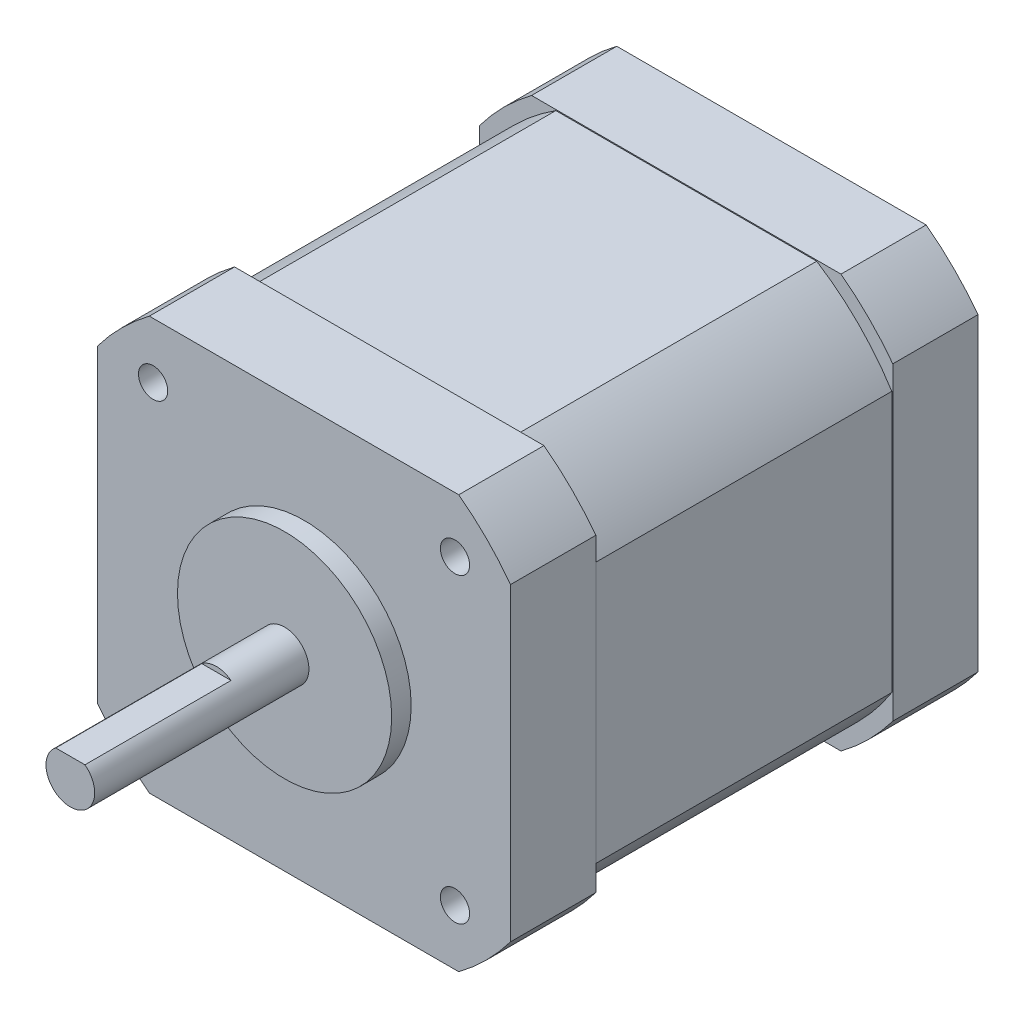
SolidWorks part; units mm, degrees
material "Plain Carbon Steel"
ref_plane "Front" through (0, 0, 0) normal (0, 0, 1) x (1, 0, 0)
ref_plane "Top" through (0, 0, 0) normal (0, 1, 0) x (1, 0, 0)
ref_plane "Right" through (0, 0, 0) normal (1, 0, 0) x (0, 0, -1)
sketch "Sketch1" plane through (0, 0, 0) normal (0, 0, 1) x (1, 0, 0)
  circle A0 centre (0, 0) radius 2.5
  dimension "D1" = 5
extrude "Boss-Extrude1" add sketch "Sketch1" along normal blind 24
sketch "Sketch2" plane through (0, 0, 0) normal (0, 0, -1) x (-1, 0, 0)
  circle A0 centre (0, 0) radius 11
  dimension "D1" = 22
extrude "Boss-Extrude2" add sketch "Sketch2" against normal blind 2
sketch "Sketch3" plane through (0, 0, 0) normal (0, 0, -1) x (-1, 0, 0)
  line L1 (21.209, -21.209) -> (-21.209, -21.209)
  line L2 (21.209, -21.209) -> (21.209, 21.209)
  line L3 (21.209, 21.209) -> (-21.209, 21.209)
  line L4 (-21.209, -21.209) -> (-21.209, 21.209)
  line L5 (21.209, -21.209) -> (-21.209, 21.209) construction
  line L6 (21.209, 21.209) -> (-21.209, -21.209) construction
  point P0 (0, 0)
  dimension "D1" = 42.418
extrude "Boss-Extrude3" add sketch "Sketch3" along normal blind 48
sketch "Sketch4" plane through (0, 0, -48) normal (0, 0, -1) x (-1, 0, 0)
  line L0 (-21.209, -15.888) -> (-21.209, -21.209)
  line L1 (15.888, -21.209) -> (21.209, -21.209)
  line L2 (21.209, 15.888) -> (21.209, 21.209)
  line L3 (-15.888, 21.209) -> (-21.209, 21.209)
  line L4 (-21.209, 21.209) -> (-21.209, -21.209)
  line L5 (-21.209, -21.209) -> (21.209, -21.209)
  line L6 (21.209, -21.209) -> (21.209, 21.209)
  line L7 (21.209, 21.209) -> (-21.209, 21.209)
  line L8 (-21.209, 21.209) -> (-21.209, 15.888)
  line L9 (-21.209, -21.209) -> (-15.888, -21.209)
  line L10 (21.209, -21.209) -> (21.209, -15.888)
  line L11 (21.209, 21.209) -> (15.888, 21.209)
  arc A0 (-21.209, -15.888) -> (-15.888, -21.209) centre (0, 0) ccw
  arc A1 (15.888, -21.209) -> (21.209, -15.888) centre (0, 0) ccw
  arc A2 (21.209, 15.888) -> (15.888, 21.209) centre (0, 0) ccw
  arc A3 (-15.888, 21.209) -> (-21.209, 15.888) centre (0, 0) ccw
  dimension "D2" = 26.5
  dimension "D1" = 0
extrude "Cut-Extrude1" cut sketch "Sketch4" against normal through all
hole_wizard "M3x0.5 Tapped Hole1" positions "Sketch6" profile "Sketch5" tap size "M3x0.5" standard "ANSI Metric"
sketch "Sketch6" plane through (0, 0, 0) normal (0, 0, 1) x (1, 0, 0)
  line L0 (-16.1632, 0) -> (0, 0) construction
  line L1 (0, 0) -> (0, 15.0764) construction
  point P0 (-15.5, 15.5)
  point P11 (-15.5, -15.5)
  point P12 (15.5, -15.5)
  point P13 (15.5, 15.5)
  dimension "D1" = 31
  dimension "D2" = 31
sketch "Sketch5" plane through (-15.5, 15.5, 0) normal (1, 0, 0) x (0, -1, 0)
  line L0 (0, 0) -> (0, 8.2511)
  line L1 (0, 8.2511) -> (1.25, 7.5)
  line L2 (1.25, 7.5) -> (1.25, 6)
  line L3 (1.25, 6) -> (1.5, 6)
  line L4 (1.5, 6) -> (1.5, 0)
  line L5 (1.5, 0) -> (0, 0)
  line L10 (0, 8.2511) -> (-1.25, 7.5) construction
  line L11 (0, -6.35) -> (0, 107.95) construction
  dimension "Tap Drill Dia." = 2.5
  dimension "Tap Drill Depth" = 7.5
  dimension "Thread Major Dia." = 3
  dimension "Thread Depth" = 6
  dimension "Drill Angle" = 118
sketch "Sketch7" plane through (0, 0, 24) normal (0, 0, 1) x (1, 0, 0)
  line L0 (-1.5, 2) -> (1.5, 2)
  circle A0 centre (0, 0) radius 2.5 construction
  circle A1 centre (0, 0) radius 2.5 construction
  arc A2 (1.5, 2) -> (-1.5, 2) centre (0, 0) ccw
  dimension "D1" = 4.5
extrude "Cut-Extrude2" cut sketch "Sketch7" against normal blind 15
ref_plane "Plane1" through (0, 0, -24) normal (0, 0, 1) x (1, 0, 0)
sketch "Sketch8" plane through (0, 0, -24) normal (0, 0, 1) x (1, 0, 0)
  line L0 (-13.3944, 21.109) -> (13.3944, 21.109)
  line L1 (-5.7152, 0) -> (0, 0) construction
  line L2 (0, 0) -> (0, 8.4579) construction
  line L3 (-15.888, 21.209) -> (15.888, 21.209) construction
  line L4 (-13.3944, -21.109) -> (13.3944, -21.109)
  line L5 (-21.109, 13.3944) -> (-21.109, -13.3944)
  line L6 (-21.209, -15.888) -> (-21.209, 15.888) construction
  line L7 (21.109, 13.3944) -> (21.109, -13.3944)
  line L12 (15.888, 21.209) -> (-15.888, 21.209)
  line L13 (-21.209, 15.888) -> (-21.209, -15.888)
  line L14 (-15.888, -21.209) -> (15.888, -21.209)
  line L15 (21.209, -15.888) -> (21.209, 15.888)
  line L16 (15.888, 21.209) -> (-15.888, 21.209)
  line L17 (-21.209, 15.888) -> (-21.209, -15.888)
  line L18 (-15.888, -21.209) -> (15.888, -21.209)
  line L19 (21.209, -15.888) -> (21.209, 15.888)
  arc A0 (-13.3944, 21.109) -> (-21.109, 13.3944) centre (0, 0) ccw
  arc A1 (-21.109, -13.3944) -> (-13.3944, -21.109) centre (0, 0) ccw
  arc A2 (21.109, 13.3944) -> (13.3944, 21.109) centre (0, 0) ccw
  arc A3 (13.3944, -21.109) -> (21.109, -13.3944) centre (0, 0) ccw
  arc A5 (-15.888, 21.209) -> (-21.209, 15.888) centre (0, 0) ccw
  arc A6 (-21.209, -15.888) -> (-15.888, -21.209) centre (0, 0) ccw
  arc A7 (15.888, -21.209) -> (21.209, -15.888) centre (0, 0) ccw
  arc A8 (21.209, 15.888) -> (15.888, 21.209) centre (0, 0) ccw
  arc A9 (-15.888, 21.209) -> (-21.209, 15.888) centre (0, 0) ccw
  arc A10 (-21.209, -15.888) -> (-15.888, -21.209) centre (0, 0) ccw
  arc A11 (15.888, -21.209) -> (21.209, -15.888) centre (0, 0) ccw
  arc A12 (21.209, 15.888) -> (15.888, 21.209) centre (0, 0) ccw
  dimension "D1" = 50
  dimension "D2" = 0.1
  dimension "D3" = 0.1
  dimension "D4" = 0
extrude "Cut-Extrude3" cut sketch "Sketch8" against normal offset from surface 8.75 and the other way offset from surface (15.25 mm away) 8.75 up to face at (0, 0, -48) other way up to face at (-14, 15.5, 0)
